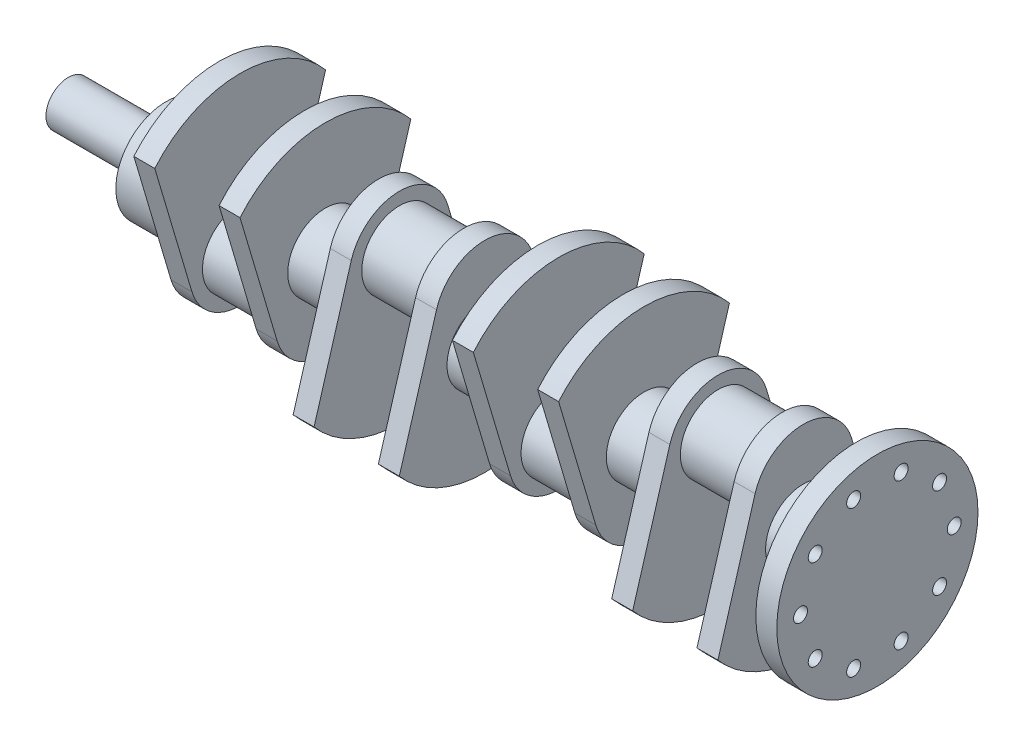
SolidWorks part; units mm, degrees
material "Gray Cast Iron"
ref_plane "Front Plane" through (0, 0, 0) normal (0, 0, 1) x (1, 0, 0)
ref_plane "Top Plane" through (0, 0, 0) normal (0, 1, 0) x (1, 0, 0)
ref_plane "Right Plane" through (0, 0, 0) normal (1, 0, 0) x (0, 0, -1)
sketch "Sketch1" plane through (0, 0, 0) normal (1, 0, 0) x (0, 0, -1)
  circle A0 centre (0, 0) radius 16
  dimension "D1" = 32
extrude "Boss-Extrude1" add sketch "Sketch1" along normal blind 70
sketch "Sketch2" plane through (70, 0, 0) normal (1, 0, 0) x (0, 0, -1)
  circle A0 centre (0, 0) radius 36
  dimension "D1" = 72
extrude "Boss-Extrude2" add sketch "Sketch2" along normal blind 38
sketch "Sketch3" plane through (108, 0, 0) normal (1, 0, 0) x (0, 0, -1)
  line L0 (34.5175, -38.2246) -> (61.1273, 51.6086)
  line L1 (-34.5175, -38.2246) -> (-61.1273, 51.6086)
  line L2 (0, -1000) -> (0, 49000) construction
  arc A0 (-34.5175, -38.2246) -> (34.5175, -38.2246) centre (0, -28) ccw
  arc A2 (61.1273, 51.6086) -> (-61.1273, 51.6086) centre (0, 0) ccw
  point P2 (0, 80)
  point P9 (0, -64)
  dimension "D1" = 72
  dimension "D2" = 80
  dimension "D3" = 144
  dimension "D4" = 33
extrude "Boss-Extrude3" add sketch "Sketch3" along normal blind 15
sketch "Sketch4" plane through (123, 0, 0) normal (1, 0, 0) x (0, 0, -1)
  circle A0 centre (0, -28) radius 27
  arc A1 (-34.5175, -38.2246) -> (34.5175, -38.2246) centre (0, -28) ccw construction
  dimension "D1" = 54
extrude "Boss-Extrude4" add sketch "Sketch4" along normal blind 46
sketch "Sketch8" plane through (169, 0, 0) normal (1, 0, 0) x (0, 0, -1)
  line L0 (34.5175, -38.2246) -> (61.1273, 51.6086) construction
  line L1 (-61.1273, 51.6086) -> (-34.5175, -38.2246) construction
  line L2 (34.5175, -38.2246) -> (61.1273, 51.6086)
  line L3 (-61.1273, 51.6086) -> (-34.5175, -38.2246)
  arc A0 (-34.5175, -38.2246) -> (34.5175, -38.2246) centre (0, -28) ccw construction
  arc A1 (61.1273, 51.6086) -> (-61.1273, 51.6086) centre (0, 0) ccw construction
  arc A2 (-34.5175, -38.2246) -> (34.5175, -38.2246) centre (0, -28) ccw
  arc A3 (61.1273, 51.6086) -> (-61.1273, 51.6086) centre (0, 0) ccw
extrude "Boss-Extrude6" add sketch "Sketch8" along normal blind 15
sketch "Sketch9" plane through (184, 0, 0) normal (1, 0, 0) x (0, 0, -1)
  circle A0 centre (0, 0) radius 27
  dimension "D1" = 54
extrude "Boss-Extrude7" add sketch "Sketch9" along normal blind 38
sketch "Sketch10" plane through (222, 0, 0) normal (1, 0, 0) x (0, 0, -1)
  line L2 (-34.5175, 38.2246) -> (-61.1273, -51.6086)
  line L3 (61.1273, -51.6086) -> (34.5175, 38.2246)
  arc A5 (34.5175, 38.2246) -> (-34.5175, 38.2246) centre (0, 28) ccw
  arc A6 (-61.1273, -51.6086) -> (61.1273, -51.6086) centre (0, 0) ccw
extrude "Boss-Extrude8" add sketch "Sketch10" along normal blind 15 separate body
sketch "Sketch12" plane through (237, 0, 0) normal (1, 0, 0) x (0, 0, -1)
  line L0 (0, -1000) -> (0, 49000) construction
  circle A0 centre (0, 28) radius 27
  arc A1 (34.5175, 38.2246) -> (-34.5175, 38.2246) centre (0, 28) ccw construction
  dimension "D1" = 54
extrude "Boss-Extrude9" add sketch "Sketch12" along normal blind 46
sketch "Sketch13" plane through (283, 0, 0) normal (1, 0, 0) x (0, 0, -1)
  line L0 (-34.5175, 38.2246) -> (-61.1273, -51.6086) construction
  line L1 (61.1273, -51.6086) -> (34.5175, 38.2246) construction
  line L2 (-34.5175, 38.2246) -> (-61.1273, -51.6086)
  line L3 (61.1273, -51.6086) -> (34.5175, 38.2246)
  arc A0 (-61.1273, -51.6086) -> (61.1273, -51.6086) centre (0, 0) ccw construction
  arc A1 (34.5175, 38.2246) -> (-34.5175, 38.2246) centre (0, 28) ccw construction
  arc A2 (-61.1273, -51.6086) -> (61.1273, -51.6086) centre (0, 0) ccw
  arc A3 (34.5175, 38.2246) -> (-34.5175, 38.2246) centre (0, 28) ccw
extrude "Boss-Extrude10" add sketch "Sketch13" along normal blind 15
sketch "Sketch15" plane through (298, 0, 0) normal (1, 0, 0) x (0, 0, -1)
  circle A0 centre (0, 0) radius 27
  dimension "D1" = 54
extrude "Boss-Extrude11" add sketch "Sketch15" along normal blind 38
sketch "Sketch16" plane through (336, 0, 0) normal (1, 0, 0) x (0, 0, -1)
  line L2 (34.5175, -38.2246) -> (61.1273, 51.6086)
  line L3 (-61.1273, 51.6086) -> (-34.5175, -38.2246)
  arc A2 (-34.5175, -38.2246) -> (34.5175, -38.2246) centre (0, -28) ccw
  arc A3 (61.1273, 51.6086) -> (-61.1273, 51.6086) centre (0, 0) ccw
extrude "Boss-Extrude12" add sketch "Sketch16" along normal blind 15
sketch "Sketch17" plane through (351, 0, 0) normal (1, 0, 0) x (0, 0, -1)
  circle A0 centre (0, -28) radius 27
  arc A1 (-34.5175, -38.2246) -> (34.5175, -38.2246) centre (0, -28) ccw construction
  dimension "D1" = 54
extrude "Boss-Extrude13" add sketch "Sketch17" along normal blind 46 contours A0
sketch "Sketch18" plane through (397, 0, 0) normal (1, 0, 0) x (0, 0, -1)
  line L0 (-61.1273, 51.6086) -> (-34.5175, -38.2246) construction
  line L1 (34.5175, -38.2246) -> (61.1273, 51.6086) construction
  line L2 (-61.1273, 51.6086) -> (-34.5175, -38.2246)
  line L3 (34.5175, -38.2246) -> (61.1273, 51.6086)
  arc A0 (61.1273, 51.6086) -> (-61.1273, 51.6086) centre (0, 0) ccw construction
  arc A1 (-34.5175, -38.2246) -> (34.5175, -38.2246) centre (0, -28) ccw construction
  arc A2 (61.1273, 51.6086) -> (-61.1273, 51.6086) centre (0, 0) ccw
  arc A3 (-34.5175, -38.2246) -> (34.5175, -38.2246) centre (0, -28) ccw
extrude "Boss-Extrude14" add sketch "Sketch18" along normal blind 15
sketch "Sketch19" plane through (412, 0, 0) normal (1, 0, 0) x (0, 0, -1)
  circle A0 centre (0, 0) radius 27
  dimension "D1" = 54
extrude "Boss-Extrude15" add sketch "Sketch19" along normal blind 38
sketch "Sketch20" plane through (450, 0, 0) normal (1, 0, 0) x (0, 0, -1)
  line L2 (-34.5175, 38.2246) -> (-61.1273, -51.6086)
  line L3 (61.1273, -51.6086) -> (34.5175, 38.2246)
  arc A2 (34.5175, 38.2246) -> (-34.5175, 38.2246) centre (0, 28) ccw
  arc A3 (-61.1273, -51.6086) -> (61.1273, -51.6086) centre (0, 0) ccw
extrude "Boss-Extrude16" add sketch "Sketch20" along normal blind 15
sketch "Sketch21" plane through (465, 0, 0) normal (1, 0, 0) x (0, 0, -1)
  circle A0 centre (0, 28) radius 27
  arc A1 (34.5175, 38.2246) -> (-34.5175, 38.2246) centre (0, 28) ccw construction
  dimension "D1" = 54
extrude "Boss-Extrude17" add sketch "Sketch21" along normal blind 46
sketch "Sketch22" plane through (511, 0, 0) normal (1, 0, 0) x (0, 0, -1)
  line L0 (-34.5175, 38.2246) -> (-61.1273, -51.6086) construction
  line L1 (61.1273, -51.6086) -> (34.5175, 38.2246) construction
  line L2 (-34.5175, 38.2246) -> (-61.1273, -51.6086)
  line L3 (61.1273, -51.6086) -> (34.5175, 38.2246)
  arc A0 (34.5175, 38.2246) -> (-34.5175, 38.2246) centre (0, 28) ccw construction
  arc A1 (-61.1273, -51.6086) -> (61.1273, -51.6086) centre (0, 0) ccw construction
  arc A2 (34.5175, 38.2246) -> (-34.5175, 38.2246) centre (0, 28) ccw
  arc A3 (-61.1273, -51.6086) -> (61.1273, -51.6086) centre (0, 0) ccw
extrude "Boss-Extrude18" add sketch "Sketch22" along normal blind 15
sketch "Sketch23" plane through (526, 0, 0) normal (1, 0, 0) x (0, 0, -1)
  circle A0 centre (0, 0) radius 27
  dimension "D1" = 54
extrude "Boss-Extrude19" add sketch "Sketch23" along normal blind 38
sketch "Sketch24" plane through (564, 0, 0) normal (1, 0, 0) x (0, 0, -1)
  circle A0 centre (0, 0) radius 72
  dimension "D1" = 144
extrude "Boss-Extrude20" add sketch "Sketch24" along normal blind 15
sketch "Sketch25" plane through (579, 0, 0) normal (1, 0, 0) x (0, 0, -1)
  line L0 (-1000, 0) -> (49000, 0) construction
  circle A0 centre (0, 0) radius 55 construction
  circle A1 centre (55, 0) radius 5
  circle A2 centre (44.4959, -32.3282) radius 5
  circle A3 centre (16.9959, -52.3081) radius 5
  circle A4 centre (-16.9959, -52.3081) radius 5
  circle A5 centre (-44.4959, -32.3282) radius 5
  circle A6 centre (-55, 0) radius 5
  circle A7 centre (-44.4959, 32.3282) radius 5
  circle A8 centre (-16.9959, 52.3081) radius 5
  circle A9 centre (16.9959, 52.3081) radius 5
  circle A10 centre (44.4959, 32.3282) radius 5
  point P27 (0, 0)
  dimension "D1" = 110
  dimension "D2" = 10
  dimension "D3" = 10
extrude "Cut-Extrude1" cut sketch "Sketch25" against normal blind 15
